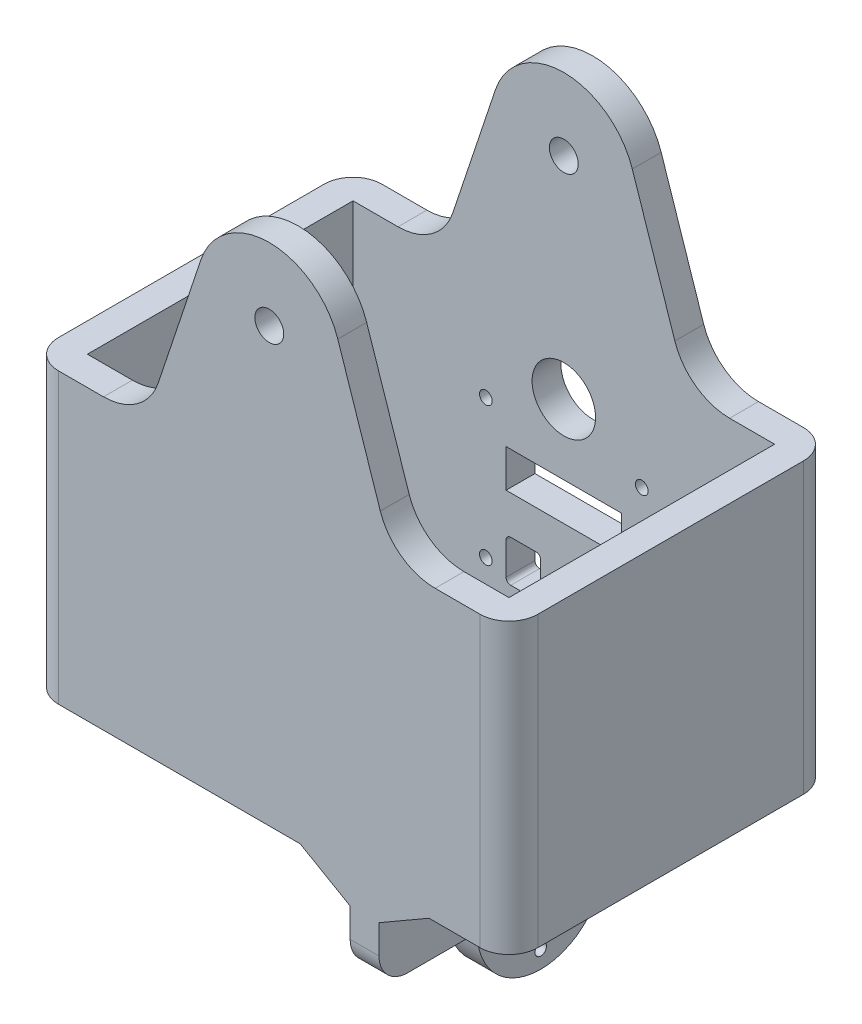
SolidWorks part; units mm, degrees
ref_plane "Front Plane" through (0, 0, 0) normal (0, 0, 1) x (1, 0, 0)
ref_plane "Top Plane" through (0, 0, 0) normal (0, 1, 0) x (1, 0, 0)
ref_plane "Right Plane" through (0, 0, 0) normal (1, 0, 0) x (0, 0, -1)
ref_plane "Plane1" through (0, 0, -16) normal (0, 0, -1) x (-1, 0, 0)
sketch "Cut" plane through (0, 0, -16) normal (0, 0, -1) x (-1, 0, 0)
  line L0 (9.2, -32.5) -> (4.8, -32.5) construction
  line L1 (10, -26.1) -> (10, -31.7) construction
  line L2 (4.8, -25.3) -> (9.2, -25.3) construction
  line L3 (4, -31.7) -> (4, -26.1) construction
  line L4 (-10, -31.7) -> (-10, -26.1) construction
  line L5 (-4.8, -32.5) -> (-9.2, -32.5) construction
  line L6 (-4, -26.1) -> (-4, -31.7) construction
  line L7 (-9.2, -25.3) -> (-4.8, -25.3) construction
  line L8 (9.2, -32.5) -> (4.8, -32.5)
  line L9 (10, -26.1) -> (10, -31.7)
  line L10 (4.8, -25.3) -> (9.2, -25.3)
  line L11 (4, -31.7) -> (4, -26.1)
  line L12 (-10, -31.7) -> (-10, -26.1)
  line L13 (-4.8, -32.5) -> (-9.2, -32.5)
  line L14 (-4, -26.1) -> (-4, -31.7)
  line L15 (-9.2, -25.3) -> (-4.8, -25.3)
  line L16 (-10, -18.65) -> (-10, -12.1) construction
  line L17 (-10, -12.1) -> (10, -12.1) construction
  line L18 (10, -12.1) -> (10, -18.65) construction
  line L19 (10, -18.65) -> (-10, -18.65) construction
  line L20 (-10, -18.65) -> (-10, -12.1)
  line L21 (-10, -12.1) -> (10, -12.1)
  line L22 (10, -12.1) -> (10, -18.65)
  line L23 (10, -18.65) -> (-10, -18.65)
  arc A0 (9.2, -32.5) -> (10, -31.7) centre (9.2, -31.7) ccw construction
  arc A1 (10, -26.1) -> (9.2, -25.3) centre (9.2, -26.1) ccw construction
  arc A2 (4, -31.7) -> (4.8, -32.5) centre (4.8, -31.7) ccw construction
  arc A3 (4.8, -25.3) -> (4, -26.1) centre (4.8, -26.1) ccw construction
  arc A4 (-9.2, -25.3) -> (-10, -26.1) centre (-9.2, -26.1) ccw construction
  arc A5 (-10, -31.7) -> (-9.2, -32.5) centre (-9.2, -31.7) ccw construction
  arc A6 (-4.8, -32.5) -> (-4, -31.7) centre (-4.8, -31.7) ccw construction
  arc A7 (-4, -26.1) -> (-4.8, -25.3) centre (-4.8, -26.1) ccw construction
  arc A8 (9.2, -32.5) -> (10, -31.7) centre (9.2, -31.7) ccw
  arc A9 (10, -26.1) -> (9.2, -25.3) centre (9.2, -26.1) ccw
  arc A10 (4, -31.7) -> (4.8, -32.5) centre (4.8, -31.7) ccw
  arc A11 (4.8, -25.3) -> (4, -26.1) centre (4.8, -26.1) ccw
  arc A12 (-9.2, -25.3) -> (-10, -26.1) centre (-9.2, -26.1) ccw
  arc A13 (-10, -31.7) -> (-9.2, -32.5) centre (-9.2, -31.7) ccw
  arc A14 (-4.8, -32.5) -> (-4, -31.7) centre (-4.8, -31.7) ccw
  arc A15 (-4, -26.1) -> (-4.8, -25.3) centre (-4.8, -26.1) ccw
  arc A16 (-5.5, 0) -> (5.5, 0) centre (0, 0) ccw construction
  arc A17 (5.5, 0) -> (-5.5, 0) centre (0, 0) ccw construction
  arc A18 (-5.5, 0) -> (5.5, 0) centre (0, 0) ccw
  arc A19 (5.5, 0) -> (-5.5, 0) centre (0, 0) ccw
  arc A20 (13.5, -7.6) -> (13.5, -5.4) centre (13.5, -6.5) ccw construction
  arc A21 (13.5, -5.4) -> (13.5, -7.6) centre (13.5, -6.5) ccw construction
  arc A22 (13.5, -31.6) -> (13.5, -29.4) centre (13.5, -30.5) ccw construction
  arc A23 (13.5, -29.4) -> (13.5, -31.6) centre (13.5, -30.5) ccw construction
  arc A24 (-13.5, -31.6) -> (-13.5, -29.4) centre (-13.5, -30.5) ccw construction
  arc A25 (-13.5, -29.4) -> (-13.5, -31.6) centre (-13.5, -30.5) ccw construction
  arc A26 (-13.5, -7.6) -> (-13.5, -5.4) centre (-13.5, -6.5) ccw construction
  arc A27 (-13.5, -5.4) -> (-13.5, -7.6) centre (-13.5, -6.5) ccw construction
  arc A28 (13.5, -7.6) -> (13.5, -5.4) centre (13.5, -6.5) ccw
  arc A29 (13.5, -5.4) -> (13.5, -7.6) centre (13.5, -6.5) ccw
  arc A30 (13.5, -31.6) -> (13.5, -29.4) centre (13.5, -30.5) ccw
  arc A31 (13.5, -29.4) -> (13.5, -31.6) centre (13.5, -30.5) ccw
  arc A32 (-13.5, -31.6) -> (-13.5, -29.4) centre (-13.5, -30.5) ccw
  arc A33 (-13.5, -29.4) -> (-13.5, -31.6) centre (-13.5, -30.5) ccw
  arc A34 (-13.5, -7.6) -> (-13.5, -5.4) centre (-13.5, -6.5) ccw
  arc A35 (-13.5, -5.4) -> (-13.5, -7.6) centre (-13.5, -6.5) ccw
sketch "Sketch3" plane through (0, 0, -16) normal (0, 0, -1) x (-1, 0, 0)
  line L0 (4.7, -38.5) -> (11.3, -38.5) construction
  line L1 (-16, 11.5) -> (16, 11.5)
  line L2 (-16, 11.5) -> (-16, -38.5)
  line L3 (-16, -38.5) -> (16, -38.5)
  line L4 (16, 11.5) -> (16, -38.5)
  line L5 (16, -9.8) -> (16, -3.2) construction
  line L6 (-7, 11.5) -> (7, 11.5) construction
  line L7 (-16, -4.525) -> (-16, -8.475) construction
extrude "Boss-Extrude1" add sketch "Sketch3" along normal blind 5
extrude "Cut-Extrude1" cut sketch "Cut" along normal blind 10
sketch "Sketch4" plane through (0, 0, -21) normal (0, 0, -1) x (-1, 0, 0)
  line L0 (-16, -38.5) -> (16, -38.5) construction
  line L1 (-16, 11.5) -> (-41.5, 11.5)
  line L2 (-16, 11.5) -> (-16, -38.5)
  line L3 (-16, -38.5) -> (-41.5, -38.5)
  line L4 (-41.5, 11.5) -> (-41.5, -38.5)
  line L5 (16, 11.5) -> (-16, 11.5) construction
  line L6 (16, -38.5) -> (41.5, -38.5)
  line L7 (16, -38.5) -> (16, 11.5)
  line L8 (16, 11.5) -> (41.5, 11.5)
  line L9 (41.5, -38.5) -> (41.5, 11.5)
  dimension "D1" = 25.5
  dimension "D2" = 25.5
extrude "Boss-Extrude2" add sketch "Sketch4" against normal blind 5
sketch "Sketch5" plane through (0, 0, -16) normal (0, 0, 1) x (1, 0, 0)
  line L0 (41.5, -38.5) -> (-41.5, -38.5) construction
  line L1 (-41.5, 11.5) -> (-36.5, 11.5)
  line L2 (-41.5, 11.5) -> (-41.5, -38.5)
  line L3 (-41.5, -38.5) -> (-36.5, -38.5)
  line L4 (-36.5, 11.5) -> (-36.5, -38.5)
  line L6 (41.5, 11.5) -> (36.5, 11.5)
  line L7 (41.5, 11.5) -> (41.5, -38.5)
  line L8 (41.5, -38.5) -> (36.5, -38.5)
  line L9 (36.5, 11.5) -> (36.5, -38.5)
  dimension "D1" = 5
  dimension "D2" = 5
extrude "Boss-Extrude3" add sketch "Sketch5" along normal blind 51
sketch "Sketch6" plane through (36.5, 0, 0) normal (-1, 0, 0) x (0, 0, 1)
  line L0 (35, -38.5) -> (-21, -38.5) construction
  line L1 (35, 11.5) -> (30, 11.5)
  line L2 (35, 11.5) -> (35, -38.5)
  line L3 (35, -38.5) -> (30, -38.5)
  line L4 (30, 11.5) -> (30, -38.5)
  dimension "D1" = 5
extrude "Boss-Extrude4" add sketch "Sketch6" along normal up to next
sketch "Sketch7" plane through (0, 0, -21) normal (0, 0, -1) x (-1, 0, 0)
  line L0 (-11.8597, 40.4493) -> (-21.5, 11.5)
  line L1 (41.5, 11.5) -> (-41.5, 11.5) construction
  line L2 (11.8597, 40.4493) -> (21.5, 11.5)
  line L3 (-41.5, 11.5) -> (-41.5, -38.5) construction
  line L4 (41.5, -38.5) -> (41.5, 11.5) construction
  line L5 (0, -38.5) -> (0, 11.5) construction
  line L6 (-41.5, -38.5) -> (41.5, -38.5) construction
  line L7 (-21.5, 11.5) -> (21.5, 11.5)
  arc A0 (11.8597, 40.4493) -> (-11.8597, 40.4493) centre (0, 36.5) ccw
  dimension "D1" = 25
  dimension "D2" = 20
  dimension "D3" = 20
  dimension "D4" = 75
extrude "Boss-Extrude5" add sketch "Sketch7" against normal blind 5
fillet "Fillet1" radius 10 2 edges at (-21.5, 11.5, -18.5) (21.5, 11.5, -18.5)
sketch "Sketch8" plane through (0, 0, 35) normal (0, 0, 1) x (1, 0, 0)
  line L0 (11.8597, 40.4493) -> (19.2221, 18.3405) construction
  line L1 (-19.2221, 18.3405) -> (-11.8597, 40.4493) construction
  line L2 (11.8597, 40.4493) -> (19.2221, 18.3405)
  line L3 (-19.2221, 18.3405) -> (-11.8597, 40.4493)
  line L4 (-28.7098, 11.5) -> (28.7098, 11.5)
  arc A0 (19.2221, 18.3405) -> (28.7098, 11.5) centre (28.7098, 21.5) ccw construction
  arc A1 (11.8597, 40.4493) -> (-11.8597, 40.4493) centre (0, 36.5) ccw construction
  arc A2 (-28.7098, 11.5) -> (-19.2221, 18.3405) centre (-28.7098, 21.5) ccw construction
  arc A3 (19.2221, 18.3405) -> (28.7098, 11.5) centre (28.7098, 21.5) ccw
  arc A4 (11.8597, 40.4493) -> (-11.8597, 40.4493) centre (0, 36.5) ccw
  arc A5 (-28.7098, 11.5) -> (-19.2221, 18.3405) centre (-28.7098, 21.5) ccw
extrude "Boss-Extrude6" add sketch "Sketch8" against normal blind 5
ref_plane "Plane2" through (16.5, 0, 0) normal (1, 0, 0) x (0, 0, -1)
sketch "Sketch9" plane through (16.5, 0, 0) normal (1, 0, 0) x (0, 0, -1)
  line L1 (-35, -38.5) -> (-30, -38.5)
  line L2 (-35, -38.5) -> (-35, -53.5)
  line L3 (-35, -53.5) -> (-30, -53.5)
  line L4 (-30, -38.5) -> (-30, -53.5)
  line L5 (21, -38.5) -> (16, -38.5)
  line L6 (21, -38.5) -> (21, -53.5)
  line L7 (21, -53.5) -> (16, -53.5)
  line L8 (16, -38.5) -> (16, -53.5)
  dimension "D1" = 15
  dimension "D2" = 15
extrude "Boss-Extrude7" add sketch "Sketch9" along normal mid plane 5
sketch "Sketch10" plane through (19, 0, 0) normal (1, 0, 0) x (0, 0, -1)
  line L0 (16, -38.5) -> (16, -53.5) construction
  line L1 (-30, -53.5) -> (-18, -53.5)
  line L2 (-30, -53.5) -> (-30, -43.5)
  line L3 (-30, -43.5) -> (-11.5826, -43.5)
  line L4 (16, -53.5) -> (16, -43.5)
  line L5 (-2.4174, -43.5) -> (16, -43.5)
  line L6 (4, -53.5) -> (16, -53.5)
  arc A0 (-18, -53.5) -> (4, -53.5) centre (-7, -53.5) ccw
  arc A1 (-2.4174, -43.5) -> (-11.5826, -43.5) centre (-7, -53.5) ccw
  dimension "D2" = 22
  dimension "D1" = 10
  dimension "D3" = 23
  dimension "D4" = 53.5
extrude "Boss-Extrude8" add sketch "Sketch10" against normal blind 5
sketch "Sketch11" plane through (19, 0, 0) normal (1, 0, 0) x (0, 0, -1)
  circle A0 centre (-7, -53.5) radius 8 construction
  circle A1 centre (-15, -53.5) radius 1
  circle A2 centre (-7, -45.5) radius 1
  circle A3 centre (1, -53.5) radius 1
  circle A4 centre (-7, -61.5) radius 1
  dimension "D1" = 16
  dimension "D2" = 2
extrude "Cut-Extrude2" cut sketch "Sketch11" against normal blind 5
fillet "Fillet4" radius 5 4 edges at (-41.5, -13.5, -21) (-41.5, -13.5, 35) (41.5, -13.5, 35) (41.5, -13.5, -21)
fillet "Fillet5" radius 5 2 edges at (16.5, -53.5, 35) (16.5, -53.5, -21)
chamfer "Chamfer1" distance 5 angle 60 2 edges at (16.5, -43.5, -16) (16.5, -43.5, 30)
fillet "Fillet6" radius 5 2 edges at (16.5, -38.5, -16) (16.5, -38.5, 30)
chamfer "Chamfer2" distance 5 angle 60 4 edges at (19, -38.5, -18.5) (14, -38.5, -18.5) (19, -38.5, 32.5) (14, -38.5, 32.5)
sketch "Sketch12" plane through (0, 0, 35) normal (0, 0, 1) x (1, 0, 0)
  circle A0 centre (0, 36.5) radius 2.5
  dimension "D1" = 5
extrude "Cut-Extrude3" cut sketch "Sketch12" against normal through all
